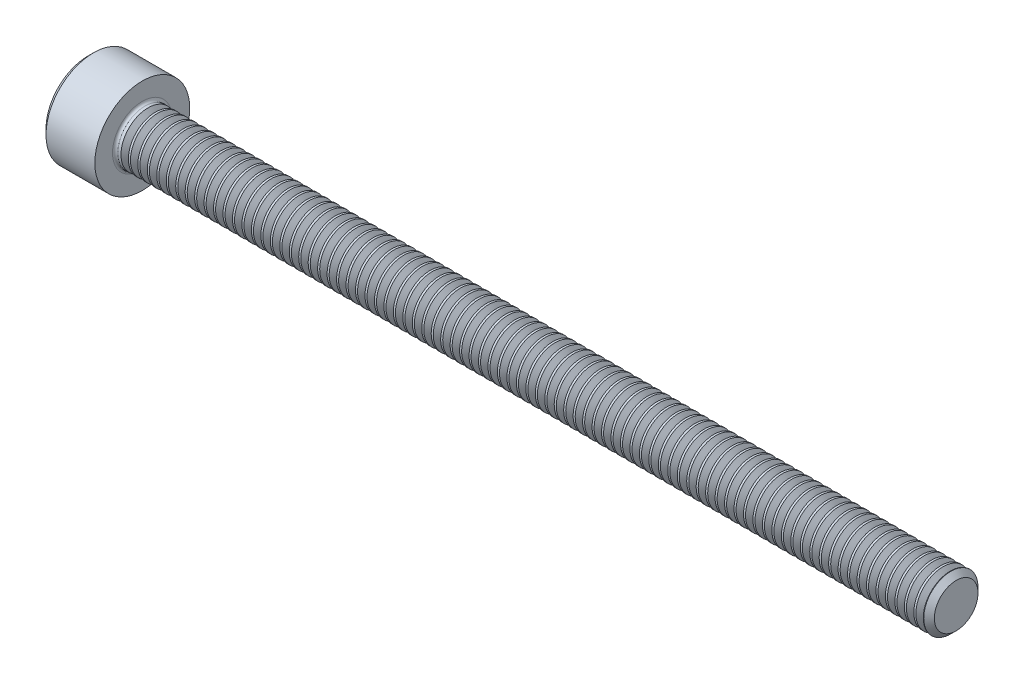
SolidWorks part; units mm, degrees
revolve "Base-Revolve" add sketch "BodySke"
sketch "BodySke" plane through (0, 0, 0) normal (0, 0, 1) x (1, 0, 0)
  line L0 (0, 0) -> (0, 3.1)
  line L1 (0.4, 3.5) -> (4, 3.5)
  line L2 (4, 3.5) -> (4, 2)
  line L3 (4, 2) -> (63.61, 2)
  line L4 (64, 1.61) -> (64, 0)
  line L5 (64, 0) -> (0, 0)
  line L6 (-31.75, 0) -> (127, 0) construction
  line L7 (0, 3.1) -> (0.4, 3.5)
  line L8 (64, 1.61) -> (63.61, 2)
  line L9 (0, -3.1) -> (0.4, -3.5) construction
  line L10 (64, -1.61) -> (63.61, -2) construction
  line L11 (4.7, 9.525) -> (4.7, 3.175) construction
  line L12 (4, 9.525) -> (4, 3.175) construction
  line L13 (14, 9.525) -> (14, 3.175) construction
  dimension "Diameter" = 4
  dimension "Head_ht" = 4
  dimension "Length" = 60
  dimension "Body_ch_ang" = 45
  dimension "Head_dia" = 7
  dimension "Head_ch_ang" = 45
  dimension "Minor_dia" = 3.22
  dimension "Advance" = 0.7
  dimension "Thread_nom" = 60
  dimension "Thread_length" = 50
  dimension "Head_ch_ht" = 0.4
cosmetic thread "ThreadCosmetic" [suppressed]
fillet "Fillet1" radius 0.2 1 edges at (4, 0, 2)
ref_plane "Plane1" through (0, 0, 0) normal (0, 0, 1) x (1, 0, 0)
ref_plane "Plane2" through (0, 0, 0) normal (0, 1, 0) x (1, 0, 0)
ref_plane "Plane3" through (0, 0, 0) normal (1, 0, 0) x (0, 0, -1)
sketch "Sketch2" plane through (0, 0, 0) normal (0, 0, 1) x (1, 0, 0)
  line L0 (0, 1.5355) -> (2, 1.5355)
  line L1 (2, 1.5355) -> (2.8865, 0)
  line L2 (-31.75, 0) -> (127, 0) construction
  line L3 (2.8865, 0) -> (0, 0)
  line L4 (0, 0) -> (0, 1.5355)
  line L5 (0, 3.1) -> (0, -3.1) construction
  line L6 (0, 0) -> (47.625, 0) construction
  line L7 (4, -3.5) -> (4, 3.5) construction
  dimension "D1" = 1.5355
  dimension "D2" = 60
revolve "Hex-PreBroach" cut sketch "Sketch2" angle 360 about L6
sketch "Sketch3" plane through (0, 0, 0) normal (-1, 0, 0) x (0, 0.5, 0.866)
  line L0 (0.8865, 1.5355) -> (-0.8865, 1.5355)
  line L1 (-0.8865, 1.5355) -> (-1.773, 0)
  line L2 (0.8865, 1.5355) -> (1.773, 0)
  line L3 (0.8865, -1.5355) -> (1.773, 0)
  line L4 (0.8865, -1.5355) -> (-0.8865, -1.5355)
  line L5 (-0.8865, -1.5355) -> (-1.773, 0)
  dimension "D1" = 1.5355
  dimension "D2" = 1.5355
  dimension "Hex_size" = 3.071
extrude "Hex" cut sketch "Sketch3" against normal blind 2
sketch "Sketch4" plane through (0, 0, 0) normal (-1, 0, 0) x (0, 0, 1)
  line L0 (0, 0) -> (1.7399, 0)
  line L1 (0, 0) -> (6.1484, 3.5498) construction
  line L2 (0, 0) -> (0.8699, 1.5068)
  line L3 (1.4457, 0.3947) -> (1.6607, 0.5189)
  line L4 (1.0647, 1.0546) -> (1.2797, 1.1788)
  arc A0 (1.4457, 0.3947) -> (1.0647, 1.0546) centre (0, 0) ccw
  arc A1 (1.7399, 0) -> (1.6607, 0.5189) centre (0, 0) ccw
  arc A2 (0.8699, 1.5068) -> (1.2797, 1.1788) centre (0, 0) cw
  dimension "D1" = 30
  dimension "D2" = 60
  dimension "Spline_p_dim" = 0.762
  dimension "D3" = 0.381
extrude "Spline" [suppressed] cut sketch "Sketch4" against normal blind 2
pattern_circular "CirPattern1" [suppressed] count 6 every 60
sketch "Sketch5" plane through (0, 0, 0) normal (0, 0, 1) x (1, 0, 0)
  line L0 (-31.75, 0) -> (127, 0) construction
  line L2 (0, 3.1) -> (0, -3.1) construction
  circle A0 centre (1.6, 0) radius 0.675
  dimension "Drilled_hole_dia" = 1.35
  dimension "Drilled_hole_loc" = 1.6
extrude "Hole" [suppressed] cut sketch "Sketch5" against normal through all and the other way through all
pattern_circular "Drilled-4" [suppressed] count 2 every 60
pattern_circular "Drilled-6" [suppressed] count 3 every 60
sketch "ThdSchSke" plane through (0, 0, 0) normal (0, 0, 1) x (1, 0, 0)
  line L0 (4.7, -1.61) -> (4.4269, -2)
  line L1 (4.7, -1.61) -> (4.9731, -2)
  line L2 (4.9731, -2) -> (4.9731, -2.5)
  line L3 (-3.175, 0) -> (5.1513, 0) construction
  line L5 (4.9731, -2.5) -> (4.4269, -2.5)
  line L6 (4.4269, -2.5) -> (4.4269, -2)
  line L7 (0, 3.1) -> (0, -3.1) construction
  dimension "Thread_minor" = 3.22
  dimension "Diameter" = 4
  dimension "Start" = 4.7
revolve "ThreadSchematic" cut sketch "ThdSchSke" angle 360 about L3
pattern_linear "ThdSchPat" count 85 spacing 0.6976 along (1, 0, 0) of "ThreadSchematic"
equation "\"D2@Sketch3\" = \"Hex_size@Sketch3\" / 2"
equation "\"D1@Sketch3\" = \"Hex_size@Sketch3\" / 2"
equation "\"D1@Sketch2\" = \"Hex_size@Sketch3\" / 2"
equation "\"D3@Sketch4\" = \"Spline_p_dim@Sketch4\" / 2"
equation "\"Thread_minor@ThreadCosmetic\"  =  \"Minor_dia@BodySke\""
equation "\"D2@CirPattern1\" = 360 / \"Num_teeth@CirPattern1\""
equation "\"Wall_thickness@Sketch2\" = \"Head_ht@BodySke\" - \"Key_eng@Hex\""
equation "\"Thread_length@ThreadCosmetic\" = ((sgn( (\"Length@BodySke\" - \"Advance@BodySke\" ) - \"Thread_nom@BodySke\" )-1)*( (\"Length@BodySke\" - \"Advance@BodySke\" ) - \"Thread_nom@BodySke\" ))/-2+ \"Thread_nom@BodySke\""
equation "\"Thread_minor@ThdSchSke\" = \"Minor_dia@BodySke\""
equation "\"Diameter@ThdSchSke\" = \"Diameter@BodySke\""
equation "\"Overcut@ThdSchSke\" = \"Diameter@BodySke\" * 1.25"
equation "\"Start@ThdSchSke\" = \"Head_ht@BodySke\" + \"Length@BodySke\" - \"Thread_length@ThreadCosmetic\"  '---Non-countersunk---"
equation "\"Num_threads@ThdSchPat\" = int( \"Thread_length@ThreadCosmetic\" / \"Advance@BodySke\" + 0.999 )  + 1"
equation "\"Advance@ThdSchPat\" = \"Thread_length@ThreadCosmetic\" /  (\"Num_threads@ThdSchPat\" - 1) 'relax it"
equation "\"Num_threads@ThdSchPat\" = \"Num_threads@ThdSchPat\" - sgn( \"Num_threads@ThdSchPat\" - 1) '---chamfered tips only---"
